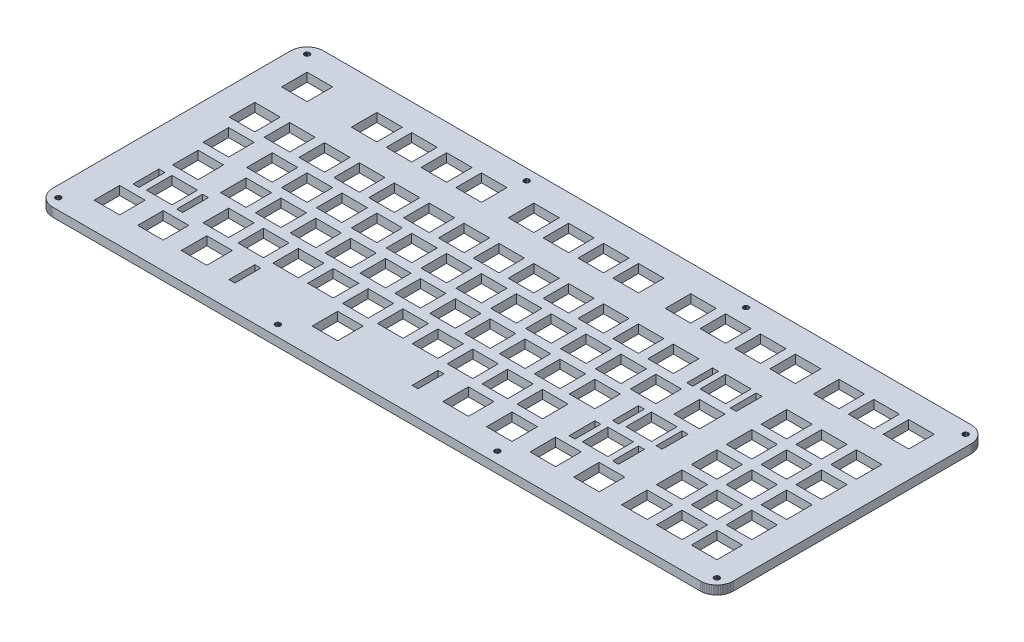
SolidWorks part; units mm, degrees
material "Acrylic (Medium-high impact)"
ref_plane "Front Plane" through (0, 0, 0) normal (0, 0, 1) x (1, 0, 0)
ref_plane "Top Plane" through (0, 0, 0) normal (0, 1, 0) x (1, 0, 0)
ref_plane "Right Plane" through (0, 0, 0) normal (1, 0, 0) x (0, 0, -1)
sketch "Sketch1" plane through (0, 0, 0) normal (0, 1, 0) x (1, 0, 0)
  line L0 (362.807, 147.967) -> (363.513, 147.941)
  line L1 (363.513, 147.941) -> (364.215, 147.857)
  line L2 (364.215, 147.857) -> (364.91, 147.719)
  line L3 (364.91, 147.719) -> (365.591, 147.527)
  line L4 (365.591, 147.527) -> (366.254, 147.282)
  line L5 (366.254, 147.282) -> (366.896, 146.987)
  line L6 (366.896, 146.987) -> (367.51, 146.641)
  line L7 (367.51, 146.641) -> (368.099, 146.25)
  line L8 (368.099, 146.25) -> (368.653, 145.812)
  line L9 (368.653, 145.812) -> (369.171, 145.331)
  line L10 (369.171, 145.331) -> (369.651, 144.812)
  line L11 (369.651, 144.812) -> (370.089, 144.259)
  line L12 (370.089, 144.259) -> (370.48, 143.67)
  line L13 (370.48, 143.67) -> (370.826, 143.053)
  line L14 (370.826, 143.053) -> (371.122, 142.412)
  line L15 (371.122, 142.412) -> (371.369, 141.749)
  line L16 (371.369, 141.749) -> (371.56, 141.07)
  line L17 (371.56, 141.07) -> (371.697, 140.375)
  line L18 (371.697, 140.375) -> (371.778, 139.674)
  line L19 (371.778, 139.674) -> (371.807, 138.967)
  line L20 (371.807, 138.967) -> (371.807, 9.0909)
  line L21 (371.807, 9.0909) -> (371.778, 8.3854)
  line L22 (371.778, 8.3854) -> (371.697, 7.684)
  line L23 (371.697, 7.684) -> (371.56, 6.9908)
  line L24 (371.56, 6.9908) -> (371.369, 6.31)
  line L25 (371.369, 6.31) -> (371.122, 5.6472)
  line L26 (371.122, 5.6472) -> (370.826, 5.0064)
  line L27 (370.826, 5.0064) -> (370.48, 4.3891)
  line L28 (370.48, 4.3891) -> (370.089, 3.8006)
  line L29 (370.089, 3.8006) -> (369.651, 3.2467)
  line L30 (369.651, 3.2467) -> (369.171, 2.7285)
  line L31 (369.171, 2.7285) -> (368.653, 2.2476)
  line L32 (368.653, 2.2476) -> (368.099, 1.8107)
  line L33 (368.099, 1.8107) -> (367.51, 1.418)
  line L34 (367.51, 1.418) -> (366.896, 1.0721)
  line L35 (366.896, 1.0721) -> (366.254, 0.7772)
  line L36 (366.254, 0.7772) -> (365.591, 0.5319)
  line L37 (365.591, 0.5319) -> (364.91, 0.3404)
  line L38 (364.91, 0.3404) -> (364.215, 0.2026)
  line L39 (364.215, 0.2026) -> (363.513, 0.1185)
  line L40 (363.513, 0.1185) -> (362.807, 0.091)
  line L41 (362.807, 0.091) -> (9.0951, 0.091)
  line L42 (9.0951, 0.091) -> (8.3881, 0.1185)
  line L43 (8.3881, 0.1185) -> (7.6867, 0.2026)
  line L44 (7.6867, 0.2026) -> (6.9922, 0.3404)
  line L45 (6.9922, 0.3404) -> (6.3128, 0.5319)
  line L46 (6.3128, 0.5319) -> (5.6499, 0.7772)
  line L47 (5.6499, 0.7772) -> (5.0092, 1.0721)
  line L48 (5.0092, 1.0721) -> (4.3918, 1.418)
  line L49 (4.3918, 1.418) -> (3.8034, 1.8107)
  line L50 (3.8034, 1.8107) -> (3.2494, 2.2476)
  line L51 (3.2494, 2.2476) -> (2.7313, 2.7285)
  line L52 (2.7313, 2.7285) -> (2.2503, 3.2467)
  line L53 (2.2503, 3.2467) -> (1.8121, 3.8006)
  line L54 (1.8121, 3.8006) -> (1.4208, 4.3891)
  line L55 (1.4208, 4.3891) -> (1.0749, 5.0064)
  line L56 (1.0749, 5.0064) -> (0.78, 5.6472)
  line L57 (0.78, 5.6472) -> (0.5347, 6.31)
  line L58 (0.5347, 6.31) -> (0.3431, 6.9908)
  line L59 (0.3431, 6.9908) -> (0.2053, 7.684)
  line L60 (0.2053, 7.684) -> (0.1213, 8.3854)
  line L61 (0.1213, 8.3854) -> (0.0937, 9.0923)
  line L62 (0.0937, 9.0923) -> (0.0951, 138.967)
  line L63 (0.0951, 138.967) -> (0.1213, 139.674)
  line L64 (0.1213, 139.674) -> (0.2053, 140.375)
  line L65 (0.2053, 140.375) -> (0.3431, 141.07)
  line L66 (0.3431, 141.07) -> (0.5347, 141.749)
  line L67 (0.5347, 141.749) -> (0.78, 142.412)
  line L68 (0.78, 142.412) -> (1.0749, 143.053)
  line L69 (1.0749, 143.053) -> (1.4208, 143.67)
  line L70 (1.4208, 143.67) -> (1.8121, 144.259)
  line L71 (1.8121, 144.259) -> (2.2503, 144.812)
  line L72 (2.2503, 144.812) -> (2.7313, 145.331)
  line L73 (2.7313, 145.331) -> (3.2494, 145.812)
  line L74 (3.2494, 145.812) -> (3.8034, 146.25)
  line L75 (3.8034, 146.25) -> (4.3918, 146.641)
  line L76 (4.3918, 146.641) -> (5.0092, 146.987)
  line L77 (5.0092, 146.987) -> (5.6499, 147.282)
  line L78 (5.6499, 147.282) -> (6.3128, 147.527)
  line L79 (6.3128, 147.527) -> (6.9922, 147.719)
  line L80 (6.9922, 147.719) -> (7.6867, 147.857)
  line L81 (7.6867, 147.857) -> (8.3881, 147.941)
  line L82 (8.3881, 147.941) -> (9.0951, 147.968)
  line L83 (9.0951, 147.968) -> (362.807, 147.967)
  line L84 (365.326, 7.5186) -> (364.917, 7.3119)
  line L85 (364.917, 7.3119) -> (364.589, 6.9825)
  line L86 (364.589, 6.9825) -> (364.381, 6.5719)
  line L87 (364.381, 6.5719) -> (364.307, 6.1157)
  line L88 (364.307, 6.1157) -> (364.381, 5.661)
  line L89 (364.381, 5.661) -> (364.589, 5.2503)
  line L90 (364.589, 5.2503) -> (364.917, 4.9237)
  line L91 (364.917, 4.9237) -> (365.326, 4.7143)
  line L92 (365.326, 4.7143) -> (365.781, 4.6413)
  line L93 (365.781, 4.6413) -> (366.24, 4.7143)
  line L94 (366.24, 4.7143) -> (366.649, 4.9237)
  line L95 (366.649, 4.9237) -> (366.977, 5.2503)
  line L96 (366.977, 5.2503) -> (367.185, 5.661)
  line L97 (367.185, 5.661) -> (367.259, 6.1157)
  line L98 (367.259, 6.1157) -> (367.185, 6.5719)
  line L99 (367.185, 6.5719) -> (366.977, 6.9825)
  line L100 (366.977, 6.9825) -> (366.649, 7.3119)
  line L101 (366.649, 7.3119) -> (366.24, 7.5186)
  line L102 (366.24, 7.5186) -> (365.781, 7.5916)
  line L103 (365.781, 7.5916) -> (365.326, 7.5186)
  line L104 (245.438, 7.5186) -> (245.027, 7.3119)
  line L105 (245.027, 7.3119) -> (244.703, 6.9825)
  line L106 (244.703, 6.9825) -> (244.492, 6.5719)
  line L107 (244.492, 6.5719) -> (244.42, 6.1157)
  line L108 (244.42, 6.1157) -> (244.492, 5.661)
  line L109 (244.492, 5.661) -> (244.703, 5.2503)
  line L110 (244.703, 5.2503) -> (245.027, 4.9237)
  line L111 (245.027, 4.9237) -> (245.438, 4.7143)
  line L112 (245.438, 4.7143) -> (245.894, 4.6413)
  line L113 (245.894, 4.6413) -> (246.35, 4.7143)
  line L114 (246.35, 4.7143) -> (246.761, 4.9237)
  line L115 (246.761, 4.9237) -> (247.088, 5.2503)
  line L116 (247.088, 5.2503) -> (247.297, 5.661)
  line L117 (247.297, 5.661) -> (247.37, 6.1157)
  line L118 (247.37, 6.1157) -> (247.297, 6.5719)
  line L119 (247.297, 6.5719) -> (247.088, 6.9825)
  line L120 (247.088, 6.9825) -> (246.761, 7.3119)
  line L121 (246.761, 7.3119) -> (246.35, 7.5186)
  line L122 (246.35, 7.5186) -> (245.894, 7.5916)
  line L123 (245.894, 7.5916) -> (245.438, 7.5186)
  line L124 (125.552, 7.5186) -> (125.138, 7.3119)
  line L125 (125.138, 7.3119) -> (124.815, 6.9825)
  line L126 (124.815, 6.9825) -> (124.604, 6.5719)
  line L127 (124.604, 6.5719) -> (124.532, 6.1157)
  line L128 (124.532, 6.1157) -> (124.604, 5.661)
  line L129 (124.604, 5.661) -> (124.815, 5.2503)
  line L130 (124.815, 5.2503) -> (125.138, 4.9237)
  line L131 (125.138, 4.9237) -> (125.552, 4.7143)
  line L132 (125.552, 4.7143) -> (126.007, 4.6413)
  line L133 (126.007, 4.6413) -> (126.463, 4.7143)
  line L134 (126.463, 4.7143) -> (126.873, 4.9237)
  line L135 (126.873, 4.9237) -> (127.201, 5.2503)
  line L136 (127.201, 5.2503) -> (127.409, 5.661)
  line L137 (127.409, 5.661) -> (127.482, 6.1157)
  line L138 (127.482, 6.1157) -> (127.409, 6.5719)
  line L139 (127.409, 6.5719) -> (127.201, 6.9825)
  line L140 (127.201, 6.9825) -> (126.873, 7.3119)
  line L141 (126.873, 7.3119) -> (126.463, 7.5186)
  line L142 (126.463, 7.5186) -> (126.007, 7.5916)
  line L143 (126.007, 7.5916) -> (125.552, 7.5186)
  line L144 (5.6637, 7.5186) -> (5.2531, 7.3119)
  line L145 (5.2531, 7.3119) -> (4.9251, 6.9825)
  line L146 (4.9251, 6.9825) -> (4.717, 6.5719)
  line L147 (4.717, 6.5719) -> (4.644, 6.1157)
  line L148 (4.644, 6.1157) -> (4.717, 5.661)
  line L149 (4.717, 5.661) -> (4.9251, 5.2503)
  line L150 (4.9251, 5.2503) -> (5.2531, 4.9237)
  line L151 (5.2531, 4.9237) -> (5.6637, 4.7143)
  line L152 (5.6637, 4.7143) -> (6.1185, 4.6413)
  line L153 (6.1185, 4.6413) -> (6.5746, 4.7143)
  line L154 (6.5746, 4.7143) -> (6.9853, 4.9237)
  line L155 (6.9853, 4.9237) -> (7.3133, 5.2503)
  line L156 (7.3133, 5.2503) -> (7.5213, 5.661)
  line L157 (7.5213, 5.661) -> (7.5944, 6.1157)
  line L158 (7.5944, 6.1157) -> (7.5213, 6.5719)
  line L159 (7.5213, 6.5719) -> (7.3133, 6.9825)
  line L160 (7.3133, 6.9825) -> (6.9853, 7.3119)
  line L161 (6.9853, 7.3119) -> (6.5746, 7.5186)
  line L162 (6.5746, 7.5186) -> (6.1185, 7.5916)
  line L163 (6.1185, 7.5916) -> (5.6637, 7.5186)
  line L164 (91.4633, 28.0679) -> (94.7127, 28.0679)
  line L165 (94.7127, 28.0679) -> (94.7127, 13.9182)
  line L166 (94.7127, 13.9182) -> (91.4633, 13.9182)
  line L167 (91.4633, 13.9182) -> (91.4633, 28.0679)
  line L168 (191.463, 28.0679) -> (194.713, 28.0679)
  line L169 (194.713, 28.0679) -> (194.713, 13.9182)
  line L170 (194.713, 13.9182) -> (191.463, 13.9182)
  line L171 (191.463, 13.9182) -> (191.463, 28.0679)
  line L172 (17.0505, 28.6177) -> (31.0003, 28.6177)
  line L173 (31.0003, 28.6177) -> (31.0003, 14.6678)
  line L174 (31.0003, 14.6678) -> (17.0505, 14.6678)
  line L175 (17.0505, 14.6678) -> (17.0505, 28.6177)
  line L176 (40.863, 28.6177) -> (54.8128, 28.6177)
  line L177 (54.8128, 28.6177) -> (54.8128, 14.6678)
  line L178 (54.8128, 14.6678) -> (40.863, 14.6678)
  line L179 (40.863, 14.6678) -> (40.863, 28.6177)
  line L180 (64.6755, 28.6177) -> (78.6253, 28.6177)
  line L181 (78.6253, 28.6177) -> (78.6253, 14.6678)
  line L182 (78.6253, 14.6678) -> (64.6755, 14.6678)
  line L183 (64.6755, 14.6678) -> (64.6755, 28.6177)
  line L184 (136.113, 28.6177) -> (150.063, 28.6177)
  line L185 (150.063, 28.6177) -> (150.063, 14.6678)
  line L186 (150.063, 14.6678) -> (136.113, 14.6678)
  line L187 (136.113, 14.6678) -> (136.113, 28.6177)
  line L188 (207.55, 28.6177) -> (221.5, 28.6177)
  line L189 (221.5, 28.6177) -> (221.5, 14.6678)
  line L190 (221.5, 14.6678) -> (207.55, 14.6678)
  line L191 (207.55, 14.6678) -> (207.55, 28.6177)
  line L192 (231.363, 28.6177) -> (245.313, 28.6177)
  line L193 (245.313, 28.6177) -> (245.313, 14.6678)
  line L194 (245.313, 14.6678) -> (231.363, 14.6678)
  line L195 (231.363, 14.6678) -> (231.363, 28.6177)
  line L196 (255.175, 28.6177) -> (269.125, 28.6177)
  line L197 (269.125, 28.6177) -> (269.125, 14.6678)
  line L198 (269.125, 14.6678) -> (255.175, 14.6678)
  line L199 (255.175, 14.6678) -> (255.175, 28.6177)
  line L200 (278.988, 28.6177) -> (292.938, 28.6177)
  line L201 (292.938, 28.6177) -> (292.938, 14.6678)
  line L202 (292.938, 14.6678) -> (278.988, 14.6678)
  line L203 (278.988, 14.6678) -> (278.988, 28.6177)
  line L204 (305.182, 28.6177) -> (319.132, 28.6177)
  line L205 (319.132, 28.6177) -> (319.132, 14.6678)
  line L206 (319.132, 14.6678) -> (305.182, 14.6678)
  line L207 (305.182, 14.6678) -> (305.182, 28.6177)
  line L208 (324.232, 28.6177) -> (338.182, 28.6177)
  line L209 (338.182, 28.6177) -> (338.182, 14.6678)
  line L210 (338.182, 14.6678) -> (324.232, 14.6678)
  line L211 (324.232, 14.6678) -> (324.232, 28.6177)
  line L212 (343.282, 28.6177) -> (357.233, 28.6177)
  line L213 (357.233, 28.6177) -> (357.233, 14.6678)
  line L214 (357.233, 14.6678) -> (343.282, 14.6678)
  line L215 (343.282, 14.6678) -> (343.282, 28.6177)
  line L216 (20.0256, 47.1166) -> (23.2751, 47.1166)
  line L217 (23.2751, 47.1166) -> (23.2751, 32.9682)
  line L218 (23.2751, 32.9682) -> (20.0256, 32.9682)
  line L219 (20.0256, 32.9682) -> (20.0256, 47.1166)
  line L220 (43.8256, 47.1166) -> (47.075, 47.1166)
  line L221 (47.075, 47.1166) -> (47.075, 32.9682)
  line L222 (47.075, 32.9682) -> (43.8256, 32.9682)
  line L223 (43.8256, 32.9682) -> (43.8256, 47.1166)
  line L224 (258.151, 47.1166) -> (261.4, 47.1166)
  line L225 (261.4, 47.1166) -> (261.4, 32.9682)
  line L226 (261.4, 32.9682) -> (258.151, 32.9682)
  line L227 (258.151, 32.9682) -> (258.151, 47.1166)
  line L228 (281.951, 47.1166) -> (285.2, 47.1166)
  line L229 (285.2, 47.1166) -> (285.2, 32.9682)
  line L230 (285.2, 32.9682) -> (281.951, 32.9682)
  line L231 (281.951, 32.9682) -> (281.951, 47.1166)
  line L232 (26.5755, 47.6677) -> (40.5253, 47.6677)
  line L233 (40.5253, 47.6677) -> (40.5253, 33.7178)
  line L234 (40.5253, 33.7178) -> (26.5755, 33.7178)
  line L235 (26.5755, 33.7178) -> (26.5755, 47.6677)
  line L236 (57.5317, 47.6677) -> (71.4816, 47.6677)
  line L237 (71.4816, 47.6677) -> (71.4816, 33.7178)
  line L238 (71.4816, 33.7178) -> (57.5317, 33.7178)
  line L239 (57.5317, 33.7178) -> (57.5317, 47.6677)
  line L240 (76.5817, 47.6677) -> (90.5316, 47.6677)
  line L241 (90.5316, 47.6677) -> (90.5316, 33.7178)
  line L242 (90.5316, 33.7178) -> (76.5817, 33.7178)
  line L243 (76.5817, 33.7178) -> (76.5817, 47.6677)
  line L244 (95.6317, 47.6677) -> (109.582, 47.6677)
  line L245 (109.582, 47.6677) -> (109.582, 33.7178)
  line L246 (109.582, 33.7178) -> (95.6317, 33.7178)
  line L247 (95.6317, 33.7178) -> (95.6317, 47.6677)
  line L248 (114.682, 47.6677) -> (128.632, 47.6677)
  line L249 (128.632, 47.6677) -> (128.632, 33.7178)
  line L250 (128.632, 33.7178) -> (114.682, 33.7178)
  line L251 (114.682, 33.7178) -> (114.682, 47.6677)
  line L252 (133.732, 47.6677) -> (147.682, 47.6677)
  line L253 (147.682, 47.6677) -> (147.682, 33.7178)
  line L254 (147.682, 33.7178) -> (133.732, 33.7178)
  line L255 (133.732, 33.7178) -> (133.732, 47.6677)
  line L256 (152.782, 47.6677) -> (166.732, 47.6677)
  line L257 (166.732, 47.6677) -> (166.732, 33.7178)
  line L258 (166.732, 33.7178) -> (152.782, 33.7178)
  line L259 (152.782, 33.7178) -> (152.782, 47.6677)
  line L260 (171.832, 47.6677) -> (185.782, 47.6677)
  line L261 (185.782, 47.6677) -> (185.782, 33.7178)
  line L262 (185.782, 33.7178) -> (171.832, 33.7178)
  line L263 (171.832, 33.7178) -> (171.832, 47.6677)
  line L264 (190.882, 47.6677) -> (204.832, 47.6677)
  line L265 (204.832, 47.6677) -> (204.832, 33.7178)
  line L266 (204.832, 33.7178) -> (190.882, 33.7178)
  line L267 (190.882, 33.7178) -> (190.882, 47.6677)
  line L268 (209.932, 47.6677) -> (223.882, 47.6677)
  line L269 (223.882, 47.6677) -> (223.882, 33.7178)
  line L270 (223.882, 33.7178) -> (209.932, 33.7178)
  line L271 (209.932, 33.7178) -> (209.932, 47.6677)
  line L272 (228.982, 47.6677) -> (242.932, 47.6677)
  line L273 (242.932, 47.6677) -> (242.932, 33.7178)
  line L274 (242.932, 33.7178) -> (228.982, 33.7178)
  line L275 (228.982, 33.7178) -> (228.982, 47.6677)
  line L276 (264.7, 47.6677) -> (278.65, 47.6677)
  line L277 (278.65, 47.6677) -> (278.65, 33.7178)
  line L278 (278.65, 33.7178) -> (264.7, 33.7178)
  line L279 (264.7, 33.7178) -> (264.7, 47.6677)
  line L280 (305.182, 47.6677) -> (319.132, 47.6677)
  line L281 (319.132, 47.6677) -> (319.132, 33.7178)
  line L282 (319.132, 33.7178) -> (305.182, 33.7178)
  line L283 (305.182, 33.7178) -> (305.182, 47.6677)
  line L284 (324.232, 47.6677) -> (338.182, 47.6677)
  line L285 (338.182, 47.6677) -> (338.182, 33.7178)
  line L286 (338.182, 33.7178) -> (324.232, 33.7178)
  line L287 (324.232, 33.7178) -> (324.232, 47.6677)
  line L288 (343.282, 47.6677) -> (357.233, 47.6677)
  line L289 (357.233, 47.6677) -> (357.233, 33.7178)
  line L290 (357.233, 33.7178) -> (343.282, 33.7178)
  line L291 (343.282, 33.7178) -> (343.282, 47.6677)
  line L292 (262.913, 66.1666) -> (266.163, 66.1666)
  line L293 (266.163, 66.1666) -> (266.163, 52.0181)
  line L294 (266.163, 52.0181) -> (262.913, 52.0181)
  line L295 (262.913, 52.0181) -> (262.913, 66.1666)
  line L296 (286.713, 66.1666) -> (289.963, 66.1666)
  line L297 (289.963, 66.1666) -> (289.963, 52.0181)
  line L298 (289.963, 52.0181) -> (286.713, 52.0181)
  line L299 (286.713, 52.0181) -> (286.713, 66.1666)
  line L300 (21.813, 66.7177) -> (35.7628, 66.7177)
  line L301 (35.7628, 66.7177) -> (35.7628, 52.7678)
  line L302 (35.7628, 52.7678) -> (21.813, 52.7678)
  line L303 (21.813, 52.7678) -> (21.813, 66.7177)
  line L304 (48.0067, 66.7177) -> (61.9566, 66.7177)
  line L305 (61.9566, 66.7177) -> (61.9566, 52.7678)
  line L306 (61.9566, 52.7678) -> (48.0067, 52.7678)
  line L307 (48.0067, 52.7678) -> (48.0067, 66.7177)
  line L308 (67.0567, 66.7177) -> (81.0066, 66.7177)
  line L309 (81.0066, 66.7177) -> (81.0066, 52.7678)
  line L310 (81.0066, 52.7678) -> (67.0567, 52.7678)
  line L311 (67.0567, 52.7678) -> (67.0567, 66.7177)
  line L312 (86.1067, 66.7177) -> (100.057, 66.7177)
  line L313 (100.057, 66.7177) -> (100.057, 52.7678)
  line L314 (100.057, 52.7678) -> (86.1067, 52.7678)
  line L315 (86.1067, 52.7678) -> (86.1067, 66.7177)
  line L316 (105.157, 66.7177) -> (119.107, 66.7177)
  line L317 (119.107, 66.7177) -> (119.107, 52.7678)
  line L318 (119.107, 52.7678) -> (105.157, 52.7678)
  line L319 (105.157, 52.7678) -> (105.157, 66.7177)
  line L320 (124.207, 66.7177) -> (138.157, 66.7177)
  line L321 (138.157, 66.7177) -> (138.157, 52.7678)
  line L322 (138.157, 52.7678) -> (124.207, 52.7678)
  line L323 (124.207, 52.7678) -> (124.207, 66.7177)
  line L324 (143.257, 66.7177) -> (157.207, 66.7177)
  line L325 (157.207, 66.7177) -> (157.207, 52.7678)
  line L326 (157.207, 52.7678) -> (143.257, 52.7678)
  line L327 (143.257, 52.7678) -> (143.257, 66.7177)
  line L328 (162.307, 66.7177) -> (176.257, 66.7177)
  line L329 (176.257, 66.7177) -> (176.257, 52.7678)
  line L330 (176.257, 52.7678) -> (162.307, 52.7678)
  line L331 (162.307, 52.7678) -> (162.307, 66.7177)
  line L332 (181.357, 66.7177) -> (195.307, 66.7177)
  line L333 (195.307, 66.7177) -> (195.307, 52.7678)
  line L334 (195.307, 52.7678) -> (181.357, 52.7678)
  line L335 (181.357, 52.7678) -> (181.357, 66.7177)
  line L336 (200.407, 66.7177) -> (214.357, 66.7177)
  line L337 (214.357, 66.7177) -> (214.357, 52.7678)
  line L338 (214.357, 52.7678) -> (200.407, 52.7678)
  line L339 (200.407, 52.7678) -> (200.407, 66.7177)
  line L340 (219.457, 66.7177) -> (233.407, 66.7177)
  line L341 (233.407, 66.7177) -> (233.407, 52.7678)
  line L342 (233.407, 52.7678) -> (219.457, 52.7678)
  line L343 (219.457, 52.7678) -> (219.457, 66.7177)
  line L344 (238.507, 66.7177) -> (252.457, 66.7177)
  line L345 (252.457, 66.7177) -> (252.457, 52.7678)
  line L346 (252.457, 52.7678) -> (238.507, 52.7678)
  line L347 (238.507, 52.7678) -> (238.507, 66.7177)
  line L348 (269.463, 66.7177) -> (283.413, 66.7177)
  line L349 (283.413, 66.7177) -> (283.413, 52.7678)
  line L350 (283.413, 52.7678) -> (269.463, 52.7678)
  line L351 (269.463, 52.7678) -> (269.463, 66.7177)
  line L352 (305.182, 66.7177) -> (319.132, 66.7177)
  line L353 (319.132, 66.7177) -> (319.132, 52.7678)
  line L354 (319.132, 52.7678) -> (305.182, 52.7678)
  line L355 (305.182, 52.7678) -> (305.182, 66.7177)
  line L356 (324.232, 66.7177) -> (338.182, 66.7177)
  line L357 (338.182, 66.7177) -> (338.182, 52.7678)
  line L358 (338.182, 52.7678) -> (324.232, 52.7678)
  line L359 (324.232, 52.7678) -> (324.232, 66.7177)
  line L360 (343.282, 66.7177) -> (357.233, 66.7177)
  line L361 (357.233, 66.7177) -> (357.233, 52.7678)
  line L362 (357.233, 52.7678) -> (343.282, 52.7678)
  line L363 (343.282, 52.7678) -> (343.282, 66.7177)
  line L364 (19.4317, 85.7677) -> (33.3816, 85.7677)
  line L365 (33.3816, 85.7677) -> (33.3816, 71.8178)
  line L366 (33.3816, 71.8178) -> (19.4317, 71.8178)
  line L367 (19.4317, 71.8178) -> (19.4317, 85.7677)
  line L368 (43.2442, 85.7677) -> (57.1941, 85.7677)
  line L369 (57.1941, 85.7677) -> (57.1941, 71.8178)
  line L370 (57.1941, 71.8178) -> (43.2442, 71.8178)
  line L371 (43.2442, 71.8178) -> (43.2442, 85.7677)
  line L372 (62.2942, 85.7677) -> (76.2441, 85.7677)
  line L373 (76.2441, 85.7677) -> (76.2441, 71.8178)
  line L374 (76.2441, 71.8178) -> (62.2942, 71.8178)
  line L375 (62.2942, 71.8178) -> (62.2942, 85.7677)
  line L376 (81.3442, 85.7677) -> (95.2941, 85.7677)
  line L377 (95.2941, 85.7677) -> (95.2941, 71.8178)
  line L378 (95.2941, 71.8178) -> (81.3442, 71.8178)
  line L379 (81.3442, 71.8178) -> (81.3442, 85.7677)
  line L380 (100.394, 85.7677) -> (114.344, 85.7677)
  line L381 (114.344, 85.7677) -> (114.344, 71.8178)
  line L382 (114.344, 71.8178) -> (100.394, 71.8178)
  line L383 (100.394, 71.8178) -> (100.394, 85.7677)
  line L384 (119.444, 85.7677) -> (133.394, 85.7677)
  line L385 (133.394, 85.7677) -> (133.394, 71.8178)
  line L386 (133.394, 71.8178) -> (119.444, 71.8178)
  line L387 (119.444, 71.8178) -> (119.444, 85.7677)
  line L388 (138.494, 85.7677) -> (152.444, 85.7677)
  line L389 (152.444, 85.7677) -> (152.444, 71.8178)
  line L390 (152.444, 71.8178) -> (138.494, 71.8178)
  line L391 (138.494, 71.8178) -> (138.494, 85.7677)
  line L392 (157.544, 85.7677) -> (171.494, 85.7677)
  line L393 (171.494, 85.7677) -> (171.494, 71.8178)
  line L394 (171.494, 71.8178) -> (157.544, 71.8178)
  line L395 (157.544, 71.8178) -> (157.544, 85.7677)
  line L396 (176.594, 85.7677) -> (190.544, 85.7677)
  line L397 (190.544, 85.7677) -> (190.544, 71.8178)
  line L398 (190.544, 71.8178) -> (176.594, 71.8178)
  line L399 (176.594, 71.8178) -> (176.594, 85.7677)
  line L400 (195.644, 85.7677) -> (209.594, 85.7677)
  line L401 (209.594, 85.7677) -> (209.594, 71.8178)
  line L402 (209.594, 71.8178) -> (195.644, 71.8178)
  line L403 (195.644, 71.8178) -> (195.644, 85.7677)
  line L404 (214.694, 85.7677) -> (228.644, 85.7677)
  line L405 (228.644, 85.7677) -> (228.644, 71.8178)
  line L406 (228.644, 71.8178) -> (214.694, 71.8178)
  line L407 (214.694, 71.8178) -> (214.694, 85.7677)
  line L408 (233.744, 85.7677) -> (247.694, 85.7677)
  line L409 (247.694, 85.7677) -> (247.694, 71.8178)
  line L410 (247.694, 71.8178) -> (233.744, 71.8178)
  line L411 (233.744, 71.8178) -> (233.744, 85.7677)
  line L412 (252.794, 85.7677) -> (266.744, 85.7677)
  line L413 (266.744, 85.7677) -> (266.744, 71.8178)
  line L414 (266.744, 71.8178) -> (252.794, 71.8178)
  line L415 (252.794, 71.8178) -> (252.794, 85.7677)
  line L416 (276.607, 85.7677) -> (290.557, 85.7677)
  line L417 (290.557, 85.7677) -> (290.557, 71.8178)
  line L418 (290.557, 71.8178) -> (276.607, 71.8178)
  line L419 (276.607, 71.8178) -> (276.607, 85.7677)
  line L420 (305.182, 85.7677) -> (319.132, 85.7677)
  line L421 (319.132, 85.7677) -> (319.132, 71.8178)
  line L422 (319.132, 71.8178) -> (305.182, 71.8178)
  line L423 (305.182, 71.8178) -> (305.182, 85.7677)
  line L424 (324.232, 85.7677) -> (338.182, 85.7677)
  line L425 (338.182, 85.7677) -> (338.182, 71.8178)
  line L426 (338.182, 71.8178) -> (324.232, 71.8178)
  line L427 (324.232, 71.8178) -> (324.232, 85.7677)
  line L428 (343.282, 85.7677) -> (357.233, 85.7677)
  line L429 (357.233, 85.7677) -> (357.233, 71.8178)
  line L430 (357.233, 71.8178) -> (343.282, 71.8178)
  line L431 (343.282, 71.8178) -> (343.282, 85.7677)
  line L432 (265.295, 104.267) -> (268.545, 104.267)
  line L433 (268.545, 104.267) -> (268.545, 90.1167)
  line L434 (268.545, 90.1167) -> (265.295, 90.1167)
  line L435 (265.295, 90.1167) -> (265.295, 104.267)
  line L436 (289.094, 104.267) -> (292.345, 104.267)
  line L437 (292.345, 104.267) -> (292.345, 90.1167)
  line L438 (292.345, 90.1167) -> (289.094, 90.1167)
  line L439 (289.094, 90.1167) -> (289.094, 104.267)
  line L440 (14.6692, 104.818) -> (28.6191, 104.818)
  line L441 (28.6191, 104.818) -> (28.6191, 90.8678)
  line L442 (28.6191, 90.8678) -> (14.6692, 90.8678)
  line L443 (14.6692, 90.8678) -> (14.6692, 104.818)
  line L444 (33.7192, 104.818) -> (47.6691, 104.818)
  line L445 (47.6691, 104.818) -> (47.6691, 90.8678)
  line L446 (47.6691, 90.8678) -> (33.7192, 90.8678)
  line L447 (33.7192, 90.8678) -> (33.7192, 104.818)
  line L448 (52.7692, 104.818) -> (66.7191, 104.818)
  line L449 (66.7191, 104.818) -> (66.7191, 90.8678)
  line L450 (66.7191, 90.8678) -> (52.7692, 90.8678)
  line L451 (52.7692, 90.8678) -> (52.7692, 104.818)
  line L452 (71.8192, 104.818) -> (85.7691, 104.818)
  line L453 (85.7691, 104.818) -> (85.7691, 90.8678)
  line L454 (85.7691, 90.8678) -> (71.8192, 90.8678)
  line L455 (71.8192, 90.8678) -> (71.8192, 104.818)
  line L456 (90.8692, 104.818) -> (104.819, 104.818)
  line L457 (104.819, 104.818) -> (104.819, 90.8678)
  line L458 (104.819, 90.8678) -> (90.8692, 90.8678)
  line L459 (90.8692, 90.8678) -> (90.8692, 104.818)
  line L460 (109.919, 104.818) -> (123.869, 104.818)
  line L461 (123.869, 104.818) -> (123.869, 90.8678)
  line L462 (123.869, 90.8678) -> (109.919, 90.8678)
  line L463 (109.919, 90.8678) -> (109.919, 104.818)
  line L464 (128.969, 104.818) -> (142.919, 104.818)
  line L465 (142.919, 104.818) -> (142.919, 90.8678)
  line L466 (142.919, 90.8678) -> (128.969, 90.8678)
  line L467 (128.969, 90.8678) -> (128.969, 104.818)
  line L468 (148.019, 104.818) -> (161.969, 104.818)
  line L469 (161.969, 104.818) -> (161.969, 90.8678)
  line L470 (161.969, 90.8678) -> (148.019, 90.8678)
  line L471 (148.019, 90.8678) -> (148.019, 104.818)
  line L472 (167.069, 104.818) -> (181.019, 104.818)
  line L473 (181.019, 104.818) -> (181.019, 90.8678)
  line L474 (181.019, 90.8678) -> (167.069, 90.8678)
  line L475 (167.069, 90.8678) -> (167.069, 104.818)
  line L476 (186.119, 104.818) -> (200.069, 104.818)
  line L477 (200.069, 104.818) -> (200.069, 90.8678)
  line L478 (200.069, 90.8678) -> (186.119, 90.8678)
  line L479 (186.119, 90.8678) -> (186.119, 104.818)
  line L480 (205.169, 104.818) -> (219.119, 104.818)
  line L481 (219.119, 104.818) -> (219.119, 90.8678)
  line L482 (219.119, 90.8678) -> (205.169, 90.8678)
  line L483 (205.169, 90.8678) -> (205.169, 104.818)
  line L484 (224.219, 104.818) -> (238.169, 104.818)
  line L485 (238.169, 104.818) -> (238.169, 90.8678)
  line L486 (238.169, 90.8678) -> (224.219, 90.8678)
  line L487 (224.219, 90.8678) -> (224.219, 104.818)
  line L488 (243.269, 104.818) -> (257.219, 104.818)
  line L489 (257.219, 104.818) -> (257.219, 90.8678)
  line L490 (257.219, 90.8678) -> (243.269, 90.8678)
  line L491 (243.269, 90.8678) -> (243.269, 104.818)
  line L492 (271.844, 104.818) -> (285.794, 104.818)
  line L493 (285.794, 104.818) -> (285.794, 90.8678)
  line L494 (285.794, 90.8678) -> (271.844, 90.8678)
  line L495 (271.844, 90.8678) -> (271.844, 104.818)
  line L496 (305.182, 104.818) -> (319.132, 104.818)
  line L497 (319.132, 104.818) -> (319.132, 90.8678)
  line L498 (319.132, 90.8678) -> (305.182, 90.8678)
  line L499 (305.182, 90.8678) -> (305.182, 104.818)
  line L500 (324.232, 104.818) -> (338.182, 104.818)
  line L501 (338.182, 104.818) -> (338.182, 90.8678)
  line L502 (338.182, 90.8678) -> (324.232, 90.8678)
  line L503 (324.232, 90.8678) -> (324.232, 104.818)
  line L504 (343.282, 104.818) -> (357.233, 104.818)
  line L505 (357.233, 104.818) -> (357.233, 90.8678)
  line L506 (357.233, 90.8678) -> (343.282, 90.8678)
  line L507 (343.282, 90.8678) -> (343.282, 104.818)
  line L508 (14.6692, 133.393) -> (28.6191, 133.393)
  line L509 (28.6191, 133.393) -> (28.6191, 119.443)
  line L510 (28.6191, 119.443) -> (14.6692, 119.443)
  line L511 (14.6692, 119.443) -> (14.6692, 133.393)
  line L512 (52.7692, 133.393) -> (66.7191, 133.393)
  line L513 (66.7191, 133.393) -> (66.7191, 119.443)
  line L514 (66.7191, 119.443) -> (52.7692, 119.443)
  line L515 (52.7692, 119.443) -> (52.7692, 133.393)
  line L516 (71.8192, 133.393) -> (85.7691, 133.393)
  line L517 (85.7691, 133.393) -> (85.7691, 119.443)
  line L518 (85.7691, 119.443) -> (71.8192, 119.443)
  line L519 (71.8192, 119.443) -> (71.8192, 133.393)
  line L520 (90.8692, 133.393) -> (104.819, 133.393)
  line L521 (104.819, 133.393) -> (104.819, 119.443)
  line L522 (104.819, 119.443) -> (90.8692, 119.443)
  line L523 (90.8692, 119.443) -> (90.8692, 133.393)
  line L524 (109.919, 133.393) -> (123.869, 133.393)
  line L525 (123.869, 133.393) -> (123.869, 119.443)
  line L526 (123.869, 119.443) -> (109.919, 119.443)
  line L527 (109.919, 119.443) -> (109.919, 133.393)
  line L528 (138.494, 133.393) -> (152.444, 133.393)
  line L529 (152.444, 133.393) -> (152.444, 119.443)
  line L530 (152.444, 119.443) -> (138.494, 119.443)
  line L531 (138.494, 119.443) -> (138.494, 133.393)
  line L532 (157.544, 133.393) -> (171.494, 133.393)
  line L533 (171.494, 133.393) -> (171.494, 119.443)
  line L534 (171.494, 119.443) -> (157.544, 119.443)
  line L535 (157.544, 119.443) -> (157.544, 133.393)
  line L536 (176.594, 133.393) -> (190.544, 133.393)
  line L537 (190.544, 133.393) -> (190.544, 119.443)
  line L538 (190.544, 119.443) -> (176.594, 119.443)
  line L539 (176.594, 119.443) -> (176.594, 133.393)
  line L540 (195.644, 133.393) -> (209.594, 133.393)
  line L541 (209.594, 133.393) -> (209.594, 119.443)
  line L542 (209.594, 119.443) -> (195.644, 119.443)
  line L543 (195.644, 119.443) -> (195.644, 133.393)
  line L544 (224.219, 133.393) -> (238.169, 133.393)
  line L545 (238.169, 133.393) -> (238.169, 119.443)
  line L546 (238.169, 119.443) -> (224.219, 119.443)
  line L547 (224.219, 119.443) -> (224.219, 133.393)
  line L548 (243.269, 133.393) -> (257.219, 133.393)
  line L549 (257.219, 133.393) -> (257.219, 119.443)
  line L550 (257.219, 119.443) -> (243.269, 119.443)
  line L551 (243.269, 119.443) -> (243.269, 133.393)
  line L552 (262.319, 133.393) -> (276.269, 133.393)
  line L553 (276.269, 133.393) -> (276.269, 119.443)
  line L554 (276.269, 119.443) -> (262.319, 119.443)
  line L555 (262.319, 119.443) -> (262.319, 133.393)
  line L556 (281.369, 133.393) -> (295.319, 133.393)
  line L557 (295.319, 133.393) -> (295.319, 119.443)
  line L558 (295.319, 119.443) -> (281.369, 119.443)
  line L559 (281.369, 119.443) -> (281.369, 133.393)
  line L560 (305.182, 133.393) -> (319.132, 133.393)
  line L561 (319.132, 133.393) -> (319.132, 119.443)
  line L562 (319.132, 119.443) -> (305.182, 119.443)
  line L563 (305.182, 119.443) -> (305.182, 133.393)
  line L564 (324.232, 133.393) -> (338.182, 133.393)
  line L565 (338.182, 133.393) -> (338.182, 119.443)
  line L566 (338.182, 119.443) -> (324.232, 119.443)
  line L567 (324.232, 119.443) -> (324.232, 133.393)
  line L568 (343.282, 133.393) -> (357.233, 133.393)
  line L569 (357.233, 133.393) -> (357.233, 119.443)
  line L570 (357.233, 119.443) -> (343.282, 119.443)
  line L571 (343.282, 119.443) -> (343.282, 133.393)
  line L572 (125.552, 143.345) -> (125.138, 143.137)
  line L573 (125.138, 143.137) -> (124.815, 142.809)
  line L574 (124.815, 142.809) -> (124.604, 142.398)
  line L575 (124.604, 142.398) -> (124.532, 141.942)
  line L576 (124.532, 141.942) -> (124.604, 141.487)
  line L577 (124.604, 141.487) -> (124.815, 141.077)
  line L578 (124.815, 141.077) -> (125.138, 140.75)
  line L579 (125.138, 140.75) -> (125.552, 140.541)
  line L580 (125.552, 140.541) -> (126.007, 140.468)
  line L581 (126.007, 140.468) -> (126.463, 140.541)
  line L582 (126.463, 140.541) -> (126.873, 140.75)
  line L583 (126.873, 140.75) -> (127.201, 141.077)
  line L584 (127.201, 141.077) -> (127.409, 141.487)
  line L585 (127.409, 141.487) -> (127.482, 141.942)
  line L586 (127.482, 141.942) -> (127.409, 142.398)
  line L587 (127.409, 142.398) -> (127.201, 142.809)
  line L588 (127.201, 142.809) -> (126.873, 143.137)
  line L589 (126.873, 143.137) -> (126.463, 143.345)
  line L590 (126.463, 143.345) -> (126.007, 143.417)
  line L591 (126.007, 143.417) -> (125.552, 143.345)
  line L592 (245.438, 143.345) -> (245.027, 143.137)
  line L593 (245.027, 143.137) -> (244.703, 142.809)
  line L594 (244.703, 142.809) -> (244.492, 142.398)
  line L595 (244.492, 142.398) -> (244.42, 141.942)
  line L596 (244.42, 141.942) -> (244.492, 141.487)
  line L597 (244.492, 141.487) -> (244.703, 141.077)
  line L598 (244.703, 141.077) -> (245.027, 140.75)
  line L599 (245.027, 140.75) -> (245.438, 140.541)
  line L600 (245.438, 140.541) -> (245.894, 140.468)
  line L601 (245.894, 140.468) -> (246.35, 140.541)
  line L602 (246.35, 140.541) -> (246.761, 140.75)
  line L603 (246.761, 140.75) -> (247.088, 141.077)
  line L604 (247.088, 141.077) -> (247.297, 141.487)
  line L605 (247.297, 141.487) -> (247.37, 141.942)
  line L606 (247.37, 141.942) -> (247.297, 142.398)
  line L607 (247.297, 142.398) -> (247.088, 142.809)
  line L608 (247.088, 142.809) -> (246.761, 143.137)
  line L609 (246.761, 143.137) -> (246.35, 143.345)
  line L610 (246.35, 143.345) -> (245.894, 143.417)
  line L611 (245.894, 143.417) -> (245.438, 143.345)
  line L612 (365.326, 143.345) -> (364.917, 143.137)
  line L613 (364.917, 143.137) -> (364.589, 142.809)
  line L614 (364.589, 142.809) -> (364.381, 142.398)
  line L615 (364.381, 142.398) -> (364.307, 141.942)
  line L616 (364.307, 141.942) -> (364.381, 141.487)
  line L617 (364.381, 141.487) -> (364.589, 141.077)
  line L618 (364.589, 141.077) -> (364.917, 140.75)
  line L619 (364.917, 140.75) -> (365.326, 140.541)
  line L620 (365.326, 140.541) -> (365.781, 140.468)
  line L621 (365.781, 140.468) -> (366.24, 140.541)
  line L622 (366.24, 140.541) -> (366.649, 140.75)
  line L623 (366.649, 140.75) -> (366.977, 141.077)
  line L624 (366.977, 141.077) -> (367.185, 141.487)
  line L625 (367.185, 141.487) -> (367.259, 141.942)
  line L626 (367.259, 141.942) -> (367.185, 142.398)
  line L627 (367.185, 142.398) -> (366.977, 142.809)
  line L628 (366.977, 142.809) -> (366.649, 143.137)
  line L629 (366.649, 143.137) -> (366.24, 143.345)
  line L630 (366.24, 143.345) -> (365.781, 143.417)
  line L631 (365.781, 143.417) -> (365.326, 143.345)
  line L632 (5.6637, 143.345) -> (5.2531, 143.137)
  line L633 (5.2531, 143.137) -> (4.9251, 142.809)
  line L634 (4.9251, 142.809) -> (4.717, 142.398)
  line L635 (4.717, 142.398) -> (4.644, 141.942)
  line L636 (4.644, 141.942) -> (4.717, 141.487)
  line L637 (4.717, 141.487) -> (4.9251, 141.077)
  line L638 (4.9251, 141.077) -> (5.2531, 140.75)
  line L639 (5.2531, 140.75) -> (5.6637, 140.541)
  line L640 (5.6637, 140.541) -> (6.1185, 140.468)
  line L641 (6.1185, 140.468) -> (6.5746, 140.541)
  line L642 (6.5746, 140.541) -> (6.9853, 140.75)
  line L643 (6.9853, 140.75) -> (7.3133, 141.077)
  line L644 (7.3133, 141.077) -> (7.5213, 141.487)
  line L645 (7.5213, 141.487) -> (7.5944, 141.942)
  line L646 (7.5944, 141.942) -> (7.5213, 142.398)
  line L647 (7.5213, 142.398) -> (7.3133, 142.809)
  line L648 (7.3133, 142.809) -> (6.9853, 143.137)
  line L649 (6.9853, 143.137) -> (6.5746, 143.345)
  line L650 (6.5746, 143.345) -> (6.1185, 143.417)
  line L651 (6.1185, 143.417) -> (5.6637, 143.345)
extrude "Boss-Extrude1" add sketch "Sketch1" along normal blind 4.7625
